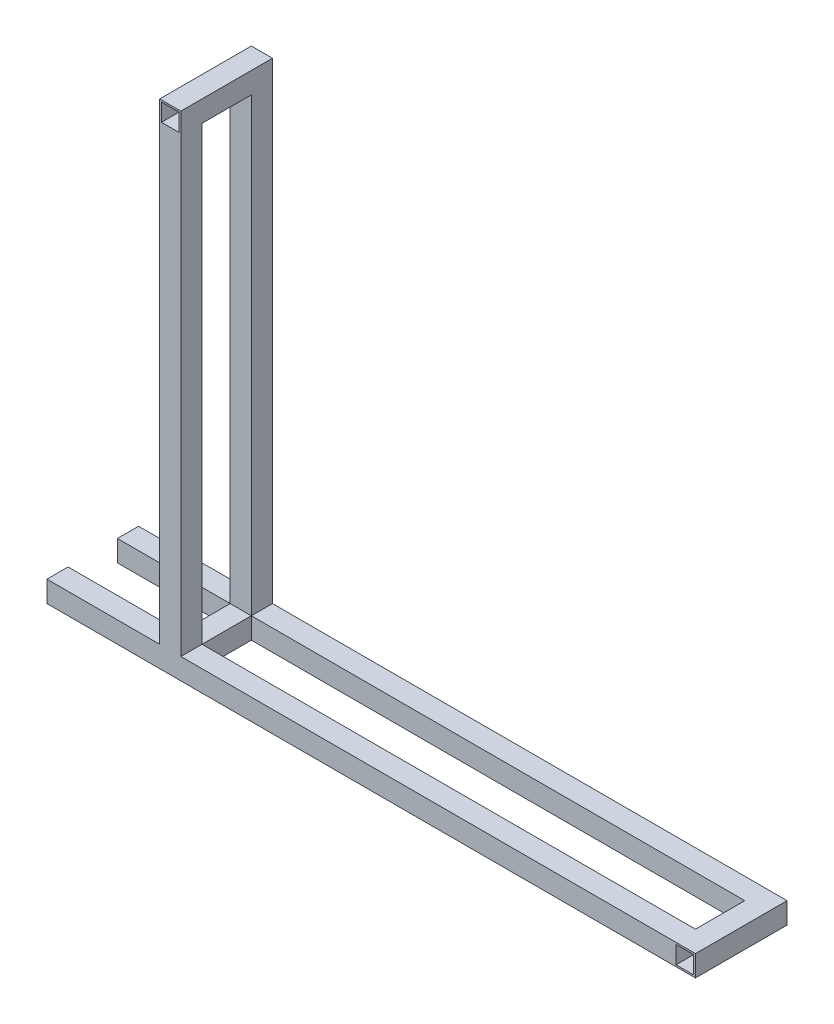
SolidWorks part; units mm, degrees
ref_plane "Alzado" through (0, 0, 0) normal (0, 0, 1) x (1, 0, 0)
ref_plane "Planta" through (0, 0, 0) normal (0, 1, 0) x (1, 0, 0)
ref_plane "Vista lateral" through (0, 0, 0) normal (1, 0, 0) x (0, 0, -1)
sketch "Croquis2" plane through (0, 0, 0) normal (0, 0, 1) x (1, 0, 0)
  line L0 (-19.05, -19.05) -> (-19.05, 406.4)
  line L2 (0, 0) -> (0, 406.4)
  line L3 (0, 406.4) -> (-19.05, 406.4)
  line L5 (0, 0) -> (444.5, 0)
  line L7 (-19.05, -19.05) -> (444.5, -19.05)
  line L8 (444.5, 0) -> (444.5, -19.05)
  dimension "D1" = 406.4
  dimension "D2" = 444.5
  dimension "D3" = 19.05
  dimension "D4" = 19.05
extrude "Saliente-Extruir1" add sketch "Croquis2" along normal mid plane 19.05
ref_plane "Plano2" through (0, 0, 53.975) normal (0, 0, 1) x (1, 0, 0)
sketch "Croquis3" plane through (0, 0, 53.975) normal (0, 0, 1) x (1, 0, 0)
  line L0 (-19.05, -19.05) -> (-19.05, 406.4)
  line L1 (-19.05, 406.4) -> (0, 406.4)
  line L2 (0, 406.4) -> (0, 0)
  line L3 (0, 0) -> (444.5, 0)
  line L4 (444.5, 0) -> (444.5, -19.05)
  line L5 (444.5, -19.05) -> (-19.05, -19.05)
extrude "Saliente-Extruir2" add sketch "Croquis3" along normal blind 19.05 separate body
sketch "Croquis9" plane through (0, 0, 73.025) normal (0, 0, 1) x (1, 0, 0)
  line L0 (0, 0) -> (0, 406.4) construction
  line L1 (-19.05, 406.4) -> (0, 406.4)
  line L2 (-19.05, 406.4) -> (-19.05, 425.45)
  line L3 (-19.05, 425.45) -> (0, 425.45)
  line L4 (0, 406.4) -> (0, 425.45)
  line L5 (-17.4625, 407.9875) -> (-17.4625, 423.8625)
  line L6 (-17.4625, 423.8625) -> (-1.5875, 423.8625)
  line L7 (-1.5875, 407.9875) -> (-1.5875, 423.8625)
  line L8 (-17.4625, 407.9875) -> (-1.5875, 407.9875)
  line L9 (444.5, -19.05) -> (463.55, -19.05)
  line L10 (444.5, -19.05) -> (444.5, 0)
  line L11 (444.5, 0) -> (463.55, 0)
  line L12 (463.55, -19.05) -> (463.55, 0)
  line L17 (-19.05, -19.05) -> (444.5, -19.05) construction
  line L18 (444.5, -19.05) -> (444.5, 0) construction
  line L19 (444.5, 0) -> (0, 0) construction
  line L20 (446.0875, -1.5875) -> (461.9625, -1.5875)
  line L21 (461.9625, -17.4625) -> (461.9625, -1.5875)
  line L22 (446.0875, -17.4625) -> (461.9625, -17.4625)
  line L23 (446.0875, -17.4625) -> (446.0875, -1.5875)
  dimension "D1" = 19.05
  dimension "D2" = 1.5875
  dimension "D3" = 19.05
  dimension "D4" = 1.5875
extrude "Saliente-Extruir6" add sketch "Croquis9" against normal up to vertex
sketch "Croquis10" plane through (0, 0, 9.525) normal (0, 0, 1) x (1, 0, 0)
  line L1 (0, 0) -> (-19.05, 0)
  line L2 (0, 0) -> (0, -19.05)
  line L3 (0, -19.05) -> (-19.05, -19.05)
  line L4 (-19.05, 0) -> (-19.05, -19.05)
extrude "Saliente-Extruir7" add sketch "Croquis10" along normal up to vertex (44.45 mm away)
sketch "Croquis11" plane through (-19.05, 0, 0) normal (-1, 0, 0) x (0, 0, 1)
  line L1 (9.525, 0) -> (-9.525, 0)
  line L2 (9.525, 0) -> (9.525, -19.05)
  line L3 (9.525, -19.05) -> (-9.525, -19.05)
  line L4 (-9.525, 0) -> (-9.525, -19.05)
  line L5 (53.975, 0) -> (73.025, 0)
  line L6 (53.975, 0) -> (53.975, -19.05)
  line L7 (53.975, -19.05) -> (73.025, -19.05)
  line L8 (73.025, 0) -> (73.025, -19.05)
extrude "Saliente-Extruir8" add sketch "Croquis11" along normal blind 101.6
sketch "Croquis12" plane through (-120.65, 0, 0) normal (-1, 0, 0) x (0, 0, 1)
  line L0 (-7.9375, -1.5875) -> (-7.9375, -17.4625)
  line L1 (-9.525, 0) -> (9.525, 0)
  line L2 (-9.525, 0) -> (-9.525, -19.05)
  line L3 (-9.525, -19.05) -> (9.525, -19.05)
  line L4 (9.525, 0) -> (9.525, -19.05)
  line L5 (-7.9375, -17.4625) -> (7.9375, -17.4625)
  line L6 (7.9375, -1.5875) -> (7.9375, -17.4625)
  line L7 (-7.9375, -1.5875) -> (7.9375, -1.5875)
  line L8 (55.5625, -1.5875) -> (55.5625, -17.4625)
  line L9 (53.975, 0) -> (73.025, 0)
  line L10 (53.975, 0) -> (53.975, -19.05)
  line L11 (53.975, -19.05) -> (73.025, -19.05)
  line L12 (73.025, 0) -> (73.025, -19.05)
  line L13 (55.5625, -17.4625) -> (71.4375, -17.4625)
  line L14 (71.4375, -1.5875) -> (71.4375, -17.4625)
  line L15 (55.5625, -1.5875) -> (71.4375, -1.5875)
  dimension "D1" = 1.5875
  dimension "D2" = 1.5875
extrude "Cortar-Extruir2" cut sketch "Croquis12" against normal up to vertex (565.15 mm away) contours L0 L5 L6 L7 | L8 L13 L14 L15
